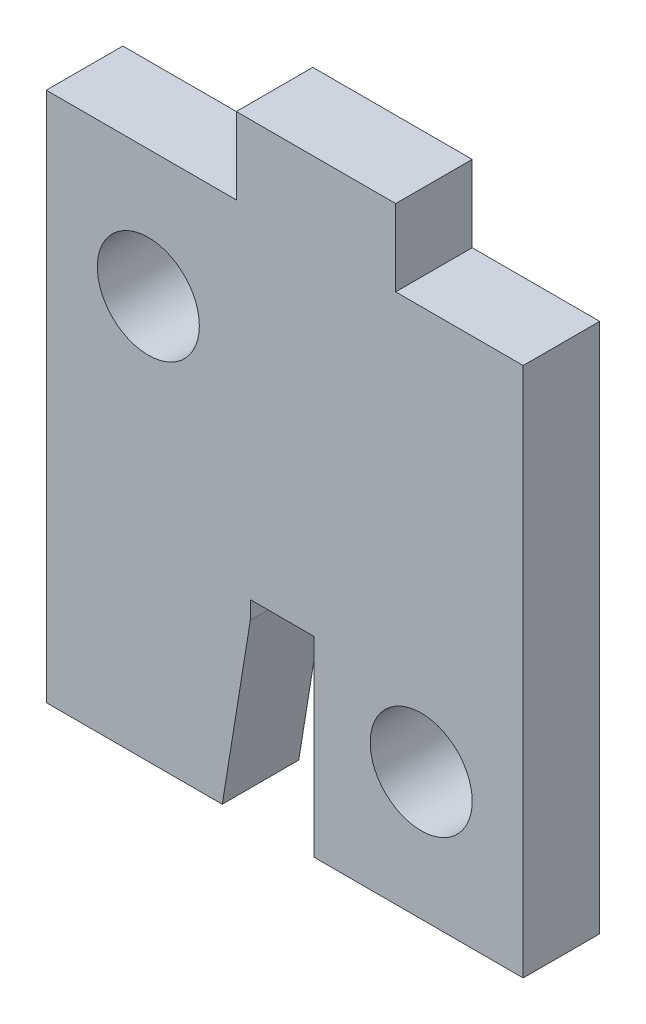
SolidWorks part; units mm, degrees
material "Acrylic (Medium-high impact)"
ref_plane "Ebene vorne" through (0, 0, 0) normal (0, 0, 1) x (1, 0, 0)
ref_plane "Ebene oben" through (0, 0, 0) normal (0, 1, 0) x (1, 0, 0)
ref_plane "Ebene rechts" through (0, 0, 0) normal (1, 0, 0) x (0, 0, -1)
sketch "Sketch1" plane through (0, 0, 0) normal (0, 0, 1) x (1, 0, 0)
  line L0 (-13.7, 0) -> (-5.7, 0)
  line L1 (-5.7, 0) -> (-5.7, 7.5)
  line L3 (-13.7, 23.8) -> (0, 23.8)
  line L4 (0, 23.8) -> (0, 0)
  line L7 (-5.7, 7.5) -> (-3.2, 7.5)
  line L8 (-3.2, 7.5) -> (-3.2, 0)
  line L9 (-3.2, 0) -> (0, 0)
  line L10 (-13.7, 0) -> (-13.7, 23.8)
  dimension "D1" = 2.5
  dimension "D2" = 13.7
  dimension "D3" = 23.8
  dimension "D4" = 7.5
  dimension "D5" = 3.2
extrude "Boss-Extrude1" add sketch "Sketch1" along normal blind 3
sketch "Sketch2" plane through (0, 0, 3) normal (0, 0, 1) x (1, 0, 0)
  line L0 (1.3, 20.8) -> (-13.7, 20.8) construction
  line L1 (-13.7, 23.8) -> (-6.25, 23.8)
  line L2 (-13.7, 23.8) -> (-13.7, 20.8)
  line L3 (-13.7, 20.8) -> (-6.25, 20.8)
  line L4 (-6.25, 23.8) -> (-6.25, 20.8)
  line L5 (0, 0) -> (0, 23.8) construction
  dimension "D1" = 6.25
extrude "Cut-Extrude1" cut sketch "Sketch2" against normal blind 3
sketch "Sketch3" plane through (0, 0, 0) normal (1, 0, 0) x (0, 0, -1)
  line L0 (0, 0) -> (0, 23.8) construction
  line L1 (-3, 0) -> (0, 0)
  line L2 (-3, 0) -> (-3, 20.8)
  line L3 (-3, 20.8) -> (0, 20.8)
  line L4 (0, 0) -> (0, 20.8)
  line L5 (-3, 23.8) -> (0, 23.8) construction
  dimension "D1" = 3
extrude "Boss-Extrude2" add sketch "Sketch3" along normal blind 5
sketch "Sketch4" plane through (0, 0, 3) normal (0, 0, 1) x (1, 0, 0)
  line L0 (-5.7, 0) -> (-6.8, 0)
  line L1 (-13.7, 0) -> (-5.7, 0) construction
  line L2 (-6.8, 0) -> (-5.7, 6.8)
  line L3 (-5.7, 0) -> (-5.7, 7.5) construction
  line L4 (-3.2, 6.8) -> (-5.7, 6.8) construction
  line L5 (-5.7, 6.8) -> (-5.7, 0)
  dimension "D1" = 1.1
extrude "Cut-Extrude2" cut sketch "Sketch4" against normal up to next
hole_wizard "Ø4.0 (4) Diameter Hole1" positions "Sketch7" profile "Sketch8" hole size "Ø4.0" standard "DIN" end condition up to next
sketch "Sketch7" plane through (0, 0, 3) normal (0, 0, 1) x (1, 0, 0)
  line L0 (-13.7, 20.8) -> (-6.25, 20.8) construction
  line L1 (-13.7, 20.8) -> (-13.7, 0) construction
  line L2 (5, 20.8) -> (5, 0) construction
  line L4 (-3.2, 0) -> (5, 0) construction
  point P0 (-9.7, 15.8)
  point P2 (1, 5)
  dimension "D1" = 5
  dimension "D2" = 4
  dimension "D3" = 4
  dimension "D4" = 5
sketch "Sketch8" plane through (-9.7, 15.8, 3) normal (1, 0, 0) x (0, -1, 0)
  line L0 (0, 0) -> (0, 3)
  line L1 (0, 3) -> (2, 3)
  line L2 (2, 3) -> (2, 0)
  line L5 (2, 0) -> (0, 0)
  line L11 (0, -6.35) -> (0, 107.95) construction
  dimension "Thru Hole Dia." = 4
  dimension "Thru Hole Depth" = 3
